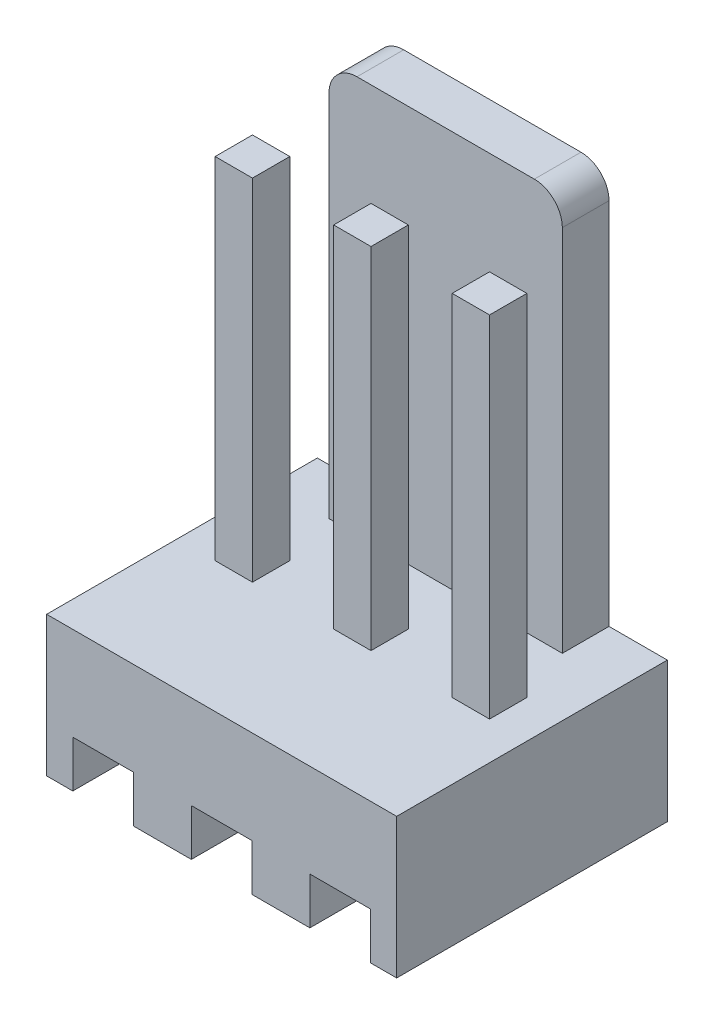
SolidWorks part; units mm, degrees
ref_plane "Alzado" through (0, 0, 0) normal (0, 0, 1) x (1, 0, 0)
ref_plane "Planta" through (0, 0, 0) normal (0, 1, 0) x (1, 0, 0)
ref_plane "Vista lateral" through (0, 0, 0) normal (1, 0, 0) x (0, 0, -1)
sketch "Croquis1" plane through (0, 0, 0) normal (0, 1, 0) x (1, 0, 0)
  line L1 (0, 0) -> (7.5, 0)
  line L2 (0, 0) -> (0, 5.8)
  line L3 (0, 5.8) -> (7.5, 5.8)
  line L4 (7.5, 0) -> (7.5, 5.8)
  dimension "D1" = 7.5
  dimension "D2" = 5.8
extrude "Extruir1" add sketch "Croquis1" along normal blind 11.5
sketch "Croquis2" plane through (7.5, 0, 0) normal (1, 0, 0) x (0, 0, -1)
  line L0 (5.8, 11.5) -> (5.8, 0) construction
  line L1 (-1.3379, 13.9586) -> (4.8, 13.9586)
  line L2 (-1.3379, 13.9586) -> (-1.3379, 3)
  line L3 (-1.3379, 3) -> (4.8, 3)
  line L4 (4.8, 13.9586) -> (4.8, 3)
  line L5 (0, 0) -> (5.8, 0) construction
  dimension "D1" = 1
  dimension "D2" = 3
extrude "Cortar-Extruir1" cut sketch "Croquis2" against normal blind 11.5
sketch "Croquis3" plane through (0, 0, -4.8) normal (0, 0, 1) x (1, 0, 0)
  line L0 (0, 3) -> (7.5, 3) construction
  line L1 (-0.9679, 11.8576) -> (1.25, 11.8576)
  line L2 (-0.9679, 11.8576) -> (-0.9679, 3)
  line L3 (-0.9679, 3) -> (1.25, 3)
  line L4 (1.25, 11.8576) -> (1.25, 3)
  line L5 (0, 11.5) -> (7.5, 11.5) construction
  line L6 (6.25, 11.8576) -> (8.9826, 11.8576)
  line L7 (6.25, 11.8576) -> (6.25, 3)
  line L8 (6.25, 3) -> (8.9826, 3)
  line L9 (8.9826, 11.8576) -> (8.9826, 3)
  line L10 (3.75, 11.5) -> (3.75, 14.0068) construction
  dimension "D1" = 5
  dimension "D2" = 2.5
extrude "Cortar-Extruir2" cut sketch "Croquis3" against normal blind 11.5
fillet "Redondeo1" radius 0.6 2 edges at (1.25, 11.5, -5.3) (6.25, 11.5, -5.3)
sketch "Croquis4" plane through (0, 3, 0) normal (0, 1, 0) x (1, 0, 0)
  line L0 (3.75, 3.6) -> (3.75, 5.2663) construction
  line L1 (3.35, 3.6) -> (4.15, 3.6)
  line L2 (3.35, 3.6) -> (3.35, 2.8)
  line L3 (3.35, 2.8) -> (4.15, 2.8)
  line L4 (4.15, 3.6) -> (4.15, 2.8)
  line L5 (6.25, 5.8) -> (6.25, 4.8) construction
  line L6 (5.65, 5.8) -> (1.85, 5.8) construction
  line L7 (5.89, 3.6) -> (6.69, 3.6)
  line L8 (5.89, 3.6) -> (5.89, 2.8)
  line L9 (5.89, 2.8) -> (6.69, 2.8)
  line L10 (6.69, 3.6) -> (6.69, 2.8)
  line L11 (0.81, 3.6) -> (0.81, 2.8)
  line L12 (1.61, 2.8) -> (0.81, 2.8)
  line L13 (1.61, 3.6) -> (1.61, 2.8)
  line L14 (1.61, 3.6) -> (0.81, 3.6)
  dimension "D1" = 0.8
  dimension "D2" = 0.8
  dimension "D3" = 2.5
  dimension "D4" = 3
extrude "Extruir2" add sketch "Croquis4" along normal blind 7.5 separate body
sketch "Croquis5" plane through (0, 0, 0) normal (0, 0, 1) x (1, 0, 0)
  line L0 (0, 0) -> (7.5, 0) construction
  line L1 (3.1, 1) -> (4.4, 1)
  line L2 (3.1, 1) -> (3.1, -0.4276)
  line L3 (3.1, -0.4276) -> (4.4, -0.4276)
  line L4 (4.4, 1) -> (4.4, -0.4276)
  line L5 (3.35, 10.5) -> (4.15, 10.5) construction
  line L6 (5.64, 1) -> (6.94, 1)
  line L7 (5.64, 1) -> (5.64, -0.4276)
  line L8 (5.64, -0.4276) -> (6.94, -0.4276)
  line L9 (6.94, 1) -> (6.94, -0.4276)
  line L10 (3.75, 10.5) -> (3.75, 12.4794) construction
  line L11 (0.56, 1) -> (0.56, -0.4276)
  line L12 (1.86, -0.4276) -> (0.56, -0.4276)
  line L13 (1.86, 1) -> (1.86, -0.4276)
  line L14 (1.86, 1) -> (0.56, 1)
  point P6 (3.75, 10.5)
  dimension "D1" = 1.3
  dimension "D2" = 1
  dimension "D3" = 0.65
extrude "Cortar-Extruir3" cut sketch "Croquis5" against normal blind 7.5
